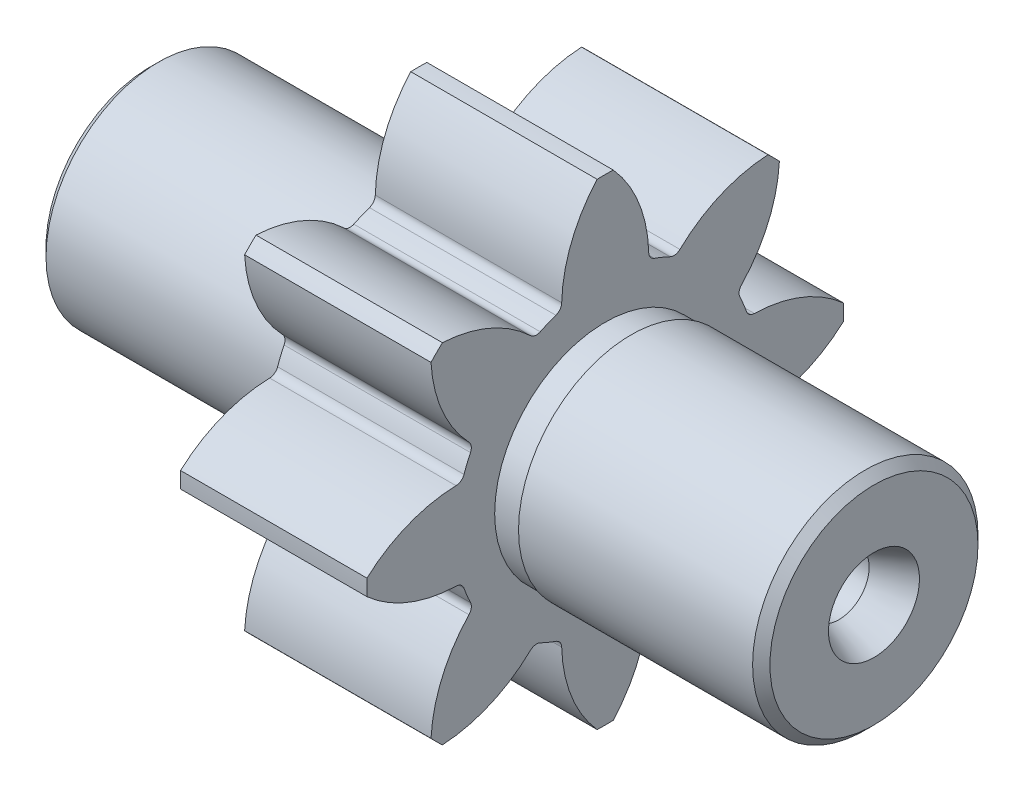
SolidWorks part; units mm, degrees
material " 40Х ГОСТ 4543-71"
ref_plane "Спереди" through (0, 0, 0) normal (0, 0, 1) x (1, 0, 0)
ref_plane "Сверху" through (0, 0, 0) normal (0, 1, 0) x (1, 0, 0)
ref_plane "Справа" through (0, 0, 0) normal (1, 0, 0) x (0, 0, -1)
sketch "Эскиз1" plane through (0, 0, 0) normal (1, 0, 0) x (0, 0, -1)
  circle A0 centre (0, 0) radius 13
  dimension "D1" = 26
extrude "Бобышка-Вытянуть1" add sketch "Эскиз1" along normal blind 31
sketch "Эскиз2" plane through (31, 0, 0) normal (1, 0, 0) x (0, 0, -1)
  circle A0 centre (0, 0) radius 17.25
  dimension "D1" = 34.5
extrude "Бобышка-Вытянуть2" add sketch "Эскиз2" along normal blind 21.5
sketch "Эскиз3" plane through (52.5, 0, 0) normal (1, 0, 0) x (0, 0, -1)
  circle A0 centre (0, 0) radius 13
  dimension "D1" = 26
extrude "Бобышка-Вытянуть3" add sketch "Эскиз3" along normal blind 31
hole_wizard "Отверстие1" positions "Эскиз5" profile "Эскиз4" legacy
sketch "Эскиз5" plane through (83.5, 0, 0) normal (1, 0, 0) x (0, 0, -1)
  point P0 (0, 0)
sketch "Эскиз4" plane through (83.5, 0, 0) normal (0, 1, 0) x (0, 0, -1)
  line L0 (0, 0) -> (0, 11.3004)
  line L1 (0, 11.3004) -> (0.5, 11)
  line L2 (0.5, 11) -> (5.25, 0)
  line L3 (5.25, 0) -> (0, 0)
  line L4 (0, -9.9017) -> (0, 117.2029) construction
  line L5 (0, 11.3004) -> (-0.5, 11) construction
  dimension "Внутренний Диаметр" = 1
  dimension "Глубина" = 11
  dimension "Наружный диаметр" = 10.5
  dimension "Угол заточки сверла" = 118
hole_wizard "Отверстие2" positions "Эскиз7" profile "Эскиз6" legacy
sketch "Эскиз7" plane through (0, 0, 0) normal (-1, 0, 0) x (0, 0, 1)
  point P0 (0, 0)
sketch "Эскиз6" plane through (0, 0, 0) normal (0, 1, 0) x (0, 0, 1)
  line L0 (0, 0) -> (0, 11.3004)
  line L1 (0, 11.3004) -> (0.5, 11)
  line L2 (0.5, 11) -> (5.25, 0)
  line L3 (5.25, 0) -> (0, 0)
  line L4 (0, -9.9017) -> (0, 117.2029) construction
  line L5 (0, 11.3004) -> (-0.5, 11) construction
  dimension "Внутренний Диаметр" = 1
  dimension "Глубина" = 11
  dimension "Наружный диаметр" = 10.5
  dimension "Угол заточки сверла" = 118
hole_wizard "Диаметр отверстия Ø7.0 (7)1" positions "Эскиз9" profile "Эскиз8" hole size "Ø7.0" standard "Din" end condition through all
sketch "Эскиз9" plane through (0, 0, 0) normal (-1, 0, 0) x (0, 0, 1)
  point P0 (0, 0)
sketch "Эскиз8" plane through (0, 0, 0) normal (0, 1, 0) x (0, 0, 1)
  line L0 (0, 0) -> (0, 83.5)
  line L1 (0, 83.5) -> (3.5, 83.5)
  line L2 (3.5, 83.5) -> (3.5, 0)
  line L5 (3.5, 0) -> (0, 0)
  line L11 (0, -6.35) -> (0, 107.95) construction
  dimension "Диаметр сквозного отверстия" = 7
  dimension "Глубина сквозного отверстия" = 83.5
sketch "Эскиз10" plane through (0, 0, 0) normal (0, 0, 1) x (1, 0, 0)
  line L0 (31, 13) -> (31, -13) construction
  line L1 (28, 15.75) -> (31, 15.75)
  line L2 (28, 15.75) -> (28, 12.75)
  line L3 (28, 12.75) -> (31, 12.75)
  line L4 (31, 15.75) -> (31, 12.75)
  line L5 (52.5, -17.25) -> (52.5, 17.25) construction
  line L6 (52.5, 15.75) -> (55.5, 15.75)
  line L7 (52.5, 15.75) -> (52.5, 12.75)
  line L8 (52.5, 12.75) -> (55.5, 12.75)
  line L9 (55.5, 15.75) -> (55.5, 12.75)
  line L10 (0, 0) -> (83.5, 0) construction
  line L11 (83.5, -13) -> (83.5, 13) construction
  dimension "D1" = 3
  dimension "D2" = 3
  dimension "D3" = 25.5
  dimension "D4" = 3
revolve "Вырез-Повернуть1" cut sketch "Эскиз10" angle 360 about L10
sketch "Эскиз11" plane through (31, 0, 0) normal (-1, 0, 0) x (0, 0, 1)
  line L0 (0, 0) -> (0, 27.5) construction
  line L1 (0, 0) -> (5.365, 26.9716) construction
  line L2 (0, 0) -> (-5.365, 26.9716) construction
  arc A0 (5.0123, 16.1821) -> (-5.0123, 16.1821) centre (0, 0) ccw
  circle A2 centre (0, 0) radius 22 construction
  arc A3 (0.9277, 27.4843) -> (-0.9277, 27.4843) centre (0, 0) ccw
  arc A4 (-0.9277, 27.4843) -> (-5.0123, 16.1821) centre (10.976, 16.7931) ccw
  arc A5 (5.0123, 16.1821) -> (0.9277, 27.4843) centre (-10.976, 16.7931) ccw
  point P3 (4.292, 21.5773)
  point P7 (-4.292, 21.5773)
  dimension "D1" = 44
  dimension "D2" = 55
  dimension "D4" = 32
  dimension "D3" = 11.25
extrude "Бобышка-Вытянуть4" add sketch "Эскиз11" against normal up to surface (21.5 mm away) up to face at (52.5, 0, 12.75)
fillet "Скругление1" radius 1 2 edges at (41.75, 16.503, -5.0214) (41.75, 16.503, 5.0214)
pattern_circular "Круговой массив1" count 8 over 360 about axis through (0, 0, 0) along (1, 0, 0) of "Бобышка-Вытянуть4", "Скругление1"
chamfer "Фаска1" distance 1 angle 45 2 edges at (83.5, 0, -13) (0, 0, -13)
